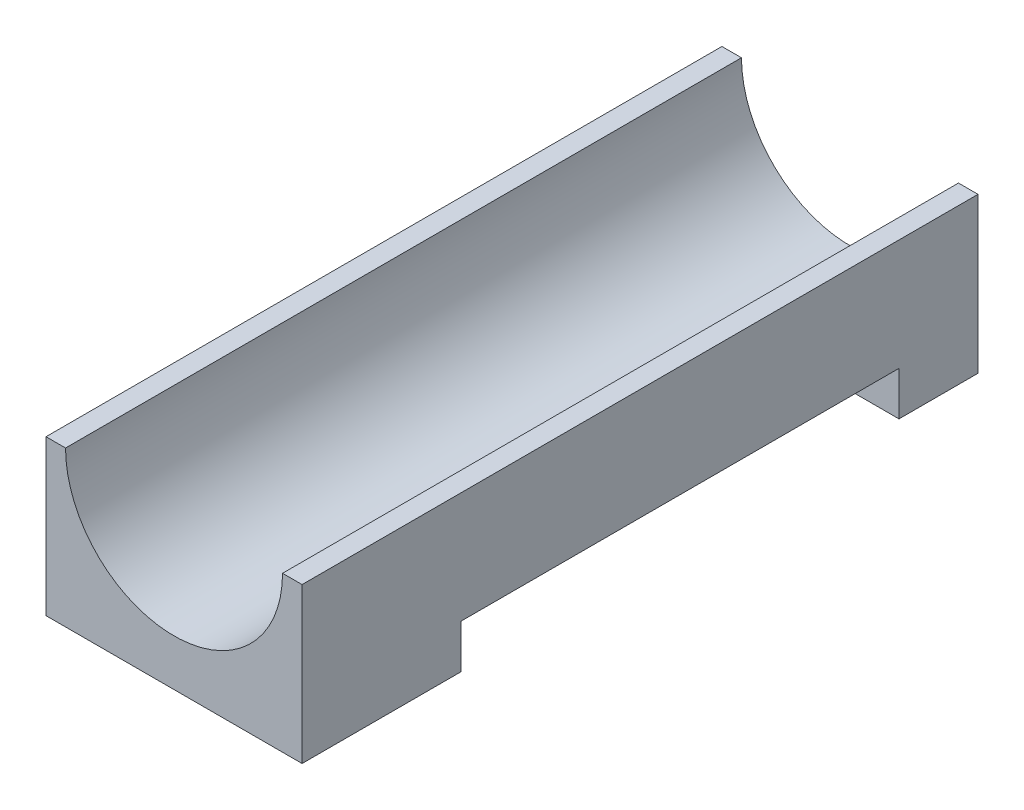
SolidWorks part; units mm, degrees
ref_plane "Face" through (0, 0, 0) normal (0, 0, 1) x (1, 0, 0)
ref_plane "Dessus" through (0, 0, 0) normal (0, 1, 0) x (1, 0, 0)
ref_plane "Droite" through (0, 0, 0) normal (1, 0, 0) x (0, 0, -1)
sketch "Esquisse1" plane through (0, 0, 0) normal (0, 0, 1) x (1, 0, 0)
  line L0 (0, 0) -> (38, 0)
  line L1 (38, 0) -> (38, 23)
  line L2 (38, 23) -> (0, 23)
  line L3 (0, 23) -> (0, 0)
  dimension "D1" = 38
  dimension "D2" = 23
extrude "Boss.-Extru.1" add sketch "Esquisse1" along normal blind 100.3
sketch "Esquisse4" plane through (0, 0, 0) normal (0, 0, 1) x (1, 0, 0)
  line L0 (38, 23) -> (0, 23) construction
  circle A0 centre (19, 23) radius 16.1
  dimension "D1" = 32.2
extrude "Enlèv. mat.-Extru.1" cut sketch "Esquisse4" along normal through all
sketch "Esquisse5" plane through (0, 0, 0) normal (1, 0, 0) x (0, 0, -1)
  line L0 (-76.725, 0) -> (-76.725, 6.5)
  line L1 (-100.3, 0) -> (0, 0) construction
  line L2 (-76.725, 6.5) -> (-11.725, 6.5)
  line L3 (-11.725, 6.5) -> (-11.725, 0)
  line L4 (-11.725, 0) -> (-76.725, 0)
  dimension "D1" = 65
  dimension "D2" = 6.5
extrude "Enlèv. mat.-Extru.2" cut sketch "Esquisse5" along normal through all
